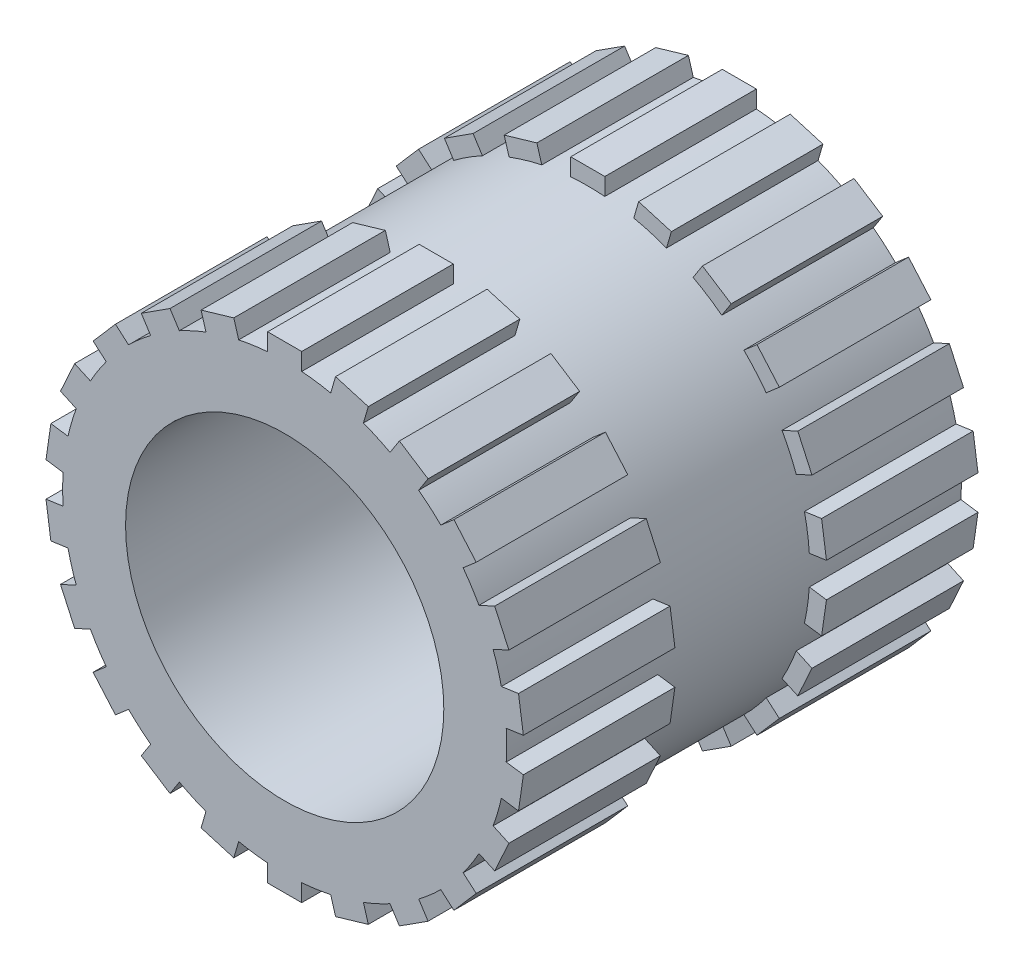
SolidWorks part; units mm, degrees
ref_plane "Front Plane" through (0, 0, 0) normal (0, 0, 1) x (1, 0, 0)
ref_plane "Top Plane" through (0, 0, 0) normal (0, 1, 0) x (1, 0, 0)
ref_plane "Right Plane" through (0, 0, 0) normal (1, 0, 0) x (0, 0, -1)
sketch "Sketch1" plane through (0, 0, 0) normal (0, 0, 1) x (1, 0, 0)
  circle A0 centre (0, 0) radius 2.93
  dimension "D1" = 5.86
extrude "Boss-Extrude1" add sketch "Sketch1" along normal mid plane 6
hole_wizard "Tap Drill for M5x0.8 Tap1" positions "Sketch2" profile "Sketch3" hole size "M5x0.8" standard "ANSI Metric" end condition through all
sketch "Sketch2" plane through (0, 0, 3) normal (0, 0, 1) x (1, 0, 0)
  point P0 (0, 0)
sketch "Sketch3" plane through (0, 0, 3) normal (1, 0, 0) x (0, -1, 0)
  line L0 (0, 0) -> (0, 6)
  line L1 (0, 6) -> (2.1, 6)
  line L2 (2.1, 6) -> (2.1, 0)
  line L5 (2.1, 0) -> (0, 0)
  line L11 (0, -6.35) -> (0, 107.95) construction
  dimension "Thru Hole Dia." = 4.2
  dimension "Thru Hole Depth" = 6
sketch "Sketch4" plane through (0, 0, 3) normal (0, 0, 1) x (1, 0, 0)
  line L0 (0, 3.15) -> (0, -3.15) construction
  line L1 (-0.225, 3.15) -> (0.225, 3.15)
  line L2 (0.225, 3.15) -> (0.225, 2.9213)
  line L3 (-0.225, 3.15) -> (-0.225, 2.9213)
  circle A0 centre (0, 0) radius 2.93 construction
  arc A1 (0.225, 2.9213) -> (-0.225, 2.9213) centre (0, 0) ccw
  dimension "D1" = 6.3
  dimension "D2" = 0.45
extrude "Boss-Extrude2" add sketch "Sketch4" against normal blind 2
pattern_circular "CirPattern1" count 22 over 360 about axis through (0, 0, 0) along (0, 0, 1) of "Boss-Extrude2"
mirror "Mirror1" about plane through (0, 0, 0) normal (0, 0, 1) of "CirPattern1", "Boss-Extrude2"
sketch "Sketch5" plane through (0, 0, 3) normal (0, 0, 1) x (1, 0, 0)
  line L0 (2.528, 1.8928) -> (2.2333, 2.2329) construction
  circle A0 centre (0, 0) radius 3.15 construction
  point P5 (2.3806, 2.0628)
  dimension "D1" = 6.3
